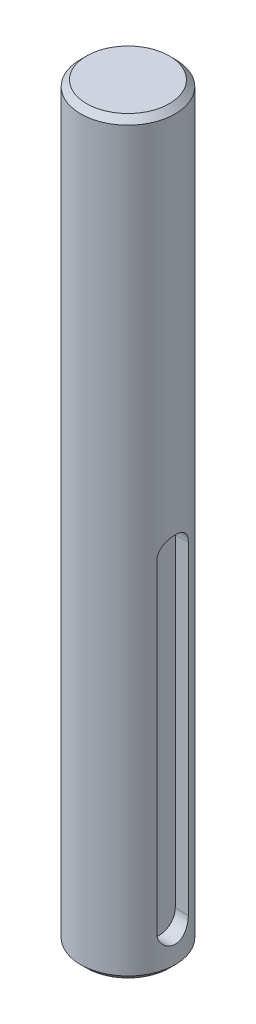
SolidWorks part; units mm, degrees
ref_plane "Front Plane" through (0, 0, 0) normal (0, 0, 1) x (1, 0, 0)
ref_plane "Top Plane" through (0, 0, 0) normal (0, 1, 0) x (1, 0, 0)
ref_plane "Right Plane" through (0, 0, 0) normal (1, 0, 0) x (0, 0, -1)
sketch "Sketch1" plane through (0, 0, 0) normal (0, 1, 0) x (1, 0, 0)
  circle A0 centre (0, 0) radius 12
  dimension "D1" = 24
extrude "Boss-Extrude1" add sketch "Sketch1" along normal blind 190
ref_plane "Plane1" through (12, 0, 0) normal (1, 0, 0) x (0, 0, -1)
sketch "Sketch2" plane through (12, 0, 0) normal (1, 0, 0) x (0, 0, -1)
  line L0 (0, 92) -> (0, 10) construction
  line L1 (4, 92) -> (4, 10)
  line L2 (-4, 92) -> (-4, 10)
  line L3 (-12, 0) -> (12, 0) construction
  arc A0 (4, 92) -> (-4, 92) centre (0, 92) ccw
  arc A1 (-4, 10) -> (4, 10) centre (0, 10) ccw
  point P3 (0, 51)
  dimension "D2" = 4
  dimension "D1" = 82
  dimension "D3" = 10
extrude "Cut-Extrude1" cut sketch "Sketch2" against normal blind 4
chamfer "Chamfer1" distance 1.5 angle 45 2 edges at (0, 0, 12) (0, 190, 12)
